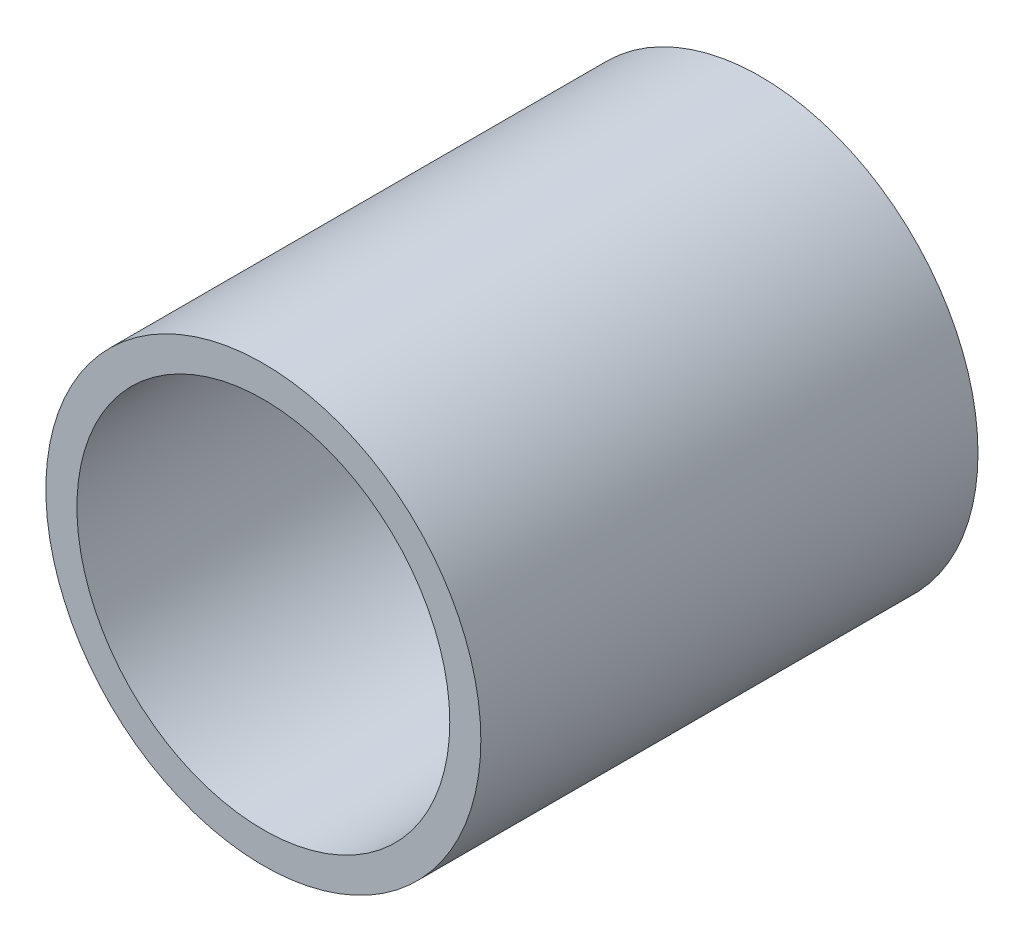
SolidWorks part; units mm, degrees
ref_plane "前视基准面" through (0, 0, 0) normal (0, 0, 1) x (1, 0, 0)
ref_plane "上视基准面" through (0, 0, 0) normal (0, 1, 0) x (1, 0, 0)
ref_plane "右视基准面" through (0, 0, 0) normal (1, 0, 0) x (0, 0, -1)
sketch "草图1" plane through (0, 0, 0) normal (0, 0, 1) x (1, 0, 0)
  circle A0 centre (0, 0) radius 1.75
  circle A1 centre (0, 0) radius 1.5
  dimension "D1" = 3.5
  dimension "D2" = 3
extrude "凸台-拉伸1" add sketch "草图1" along normal blind 4
